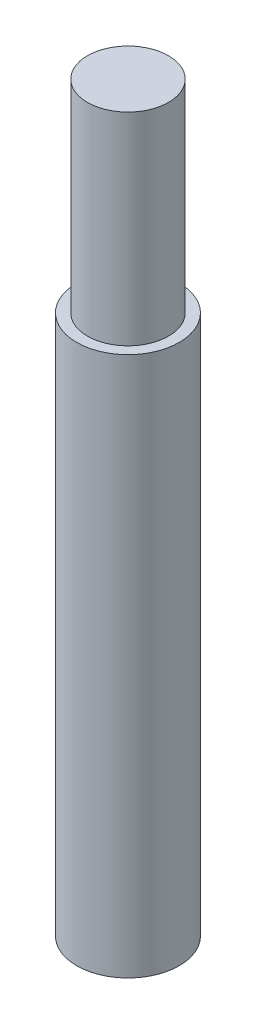
SolidWorks part; units mm, degrees
material "6061-T6 (SS)"
ref_plane "Front Plane" through (0, 0, 0) normal (0, 0, 1) x (1, 0, 0)
ref_plane "Top Plane" through (0, 0, 0) normal (0, 1, 0) x (1, 0, 0)
ref_plane "Right Plane" through (0, 0, 0) normal (1, 0, 0) x (0, 0, -1)
sketch "Sketch1" plane through (0, 0, 0) normal (0, 1, 0) x (1, 0, 0)
  circle A0 centre (0, 0) radius 2.413
  dimension "D1" = 4.826
extrude "Boss-Extrude1" add sketch "Sketch1" along normal blind 25.4
sketch "Sketch2" plane through (0, 25.4, 0) normal (0, 1, 0) x (1, 0, 0)
  circle A0 centre (0, 0) radius 1.905
  dimension "D1" = 3.81
extrude "Boss-Extrude2" add sketch "Sketch2" along normal blind 9.525
